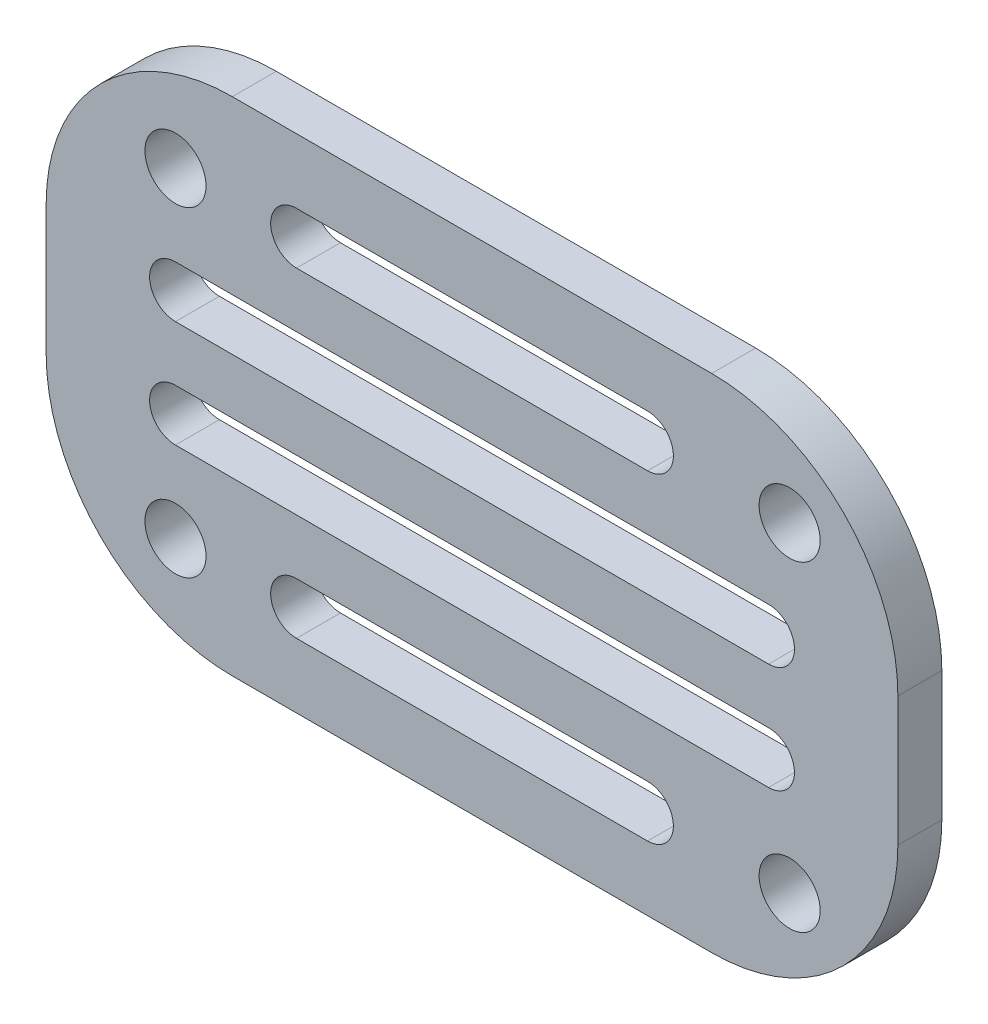
SolidWorks part; units mm, degrees
ref_plane "Front Plane" through (0, 0, 0) normal (0, 0, 1) x (1, 0, 0)
ref_plane "Top Plane" through (0, 0, 0) normal (0, 1, 0) x (1, 0, 0)
ref_plane "Right Plane" through (0, 0, 0) normal (1, 0, 0) x (0, 0, -1)
sketch "Sketch1" plane through (0, 0, 0) normal (0, 0, 1) x (1, 0, 0)
  line L0 (-12.7, -7.874) -> (17.4625, -7.874) construction
  line L5 (20.1005, -9.6408) -> (17.4625, -7.874) construction
  line L6 (-9.906, 12.319) -> (13.6347, 12.319)
  line L7 (17.4625, -7.874) -> (17.4625, 7.874) construction
  line L8 (17.4625, 7.874) -> (-12.7, 7.874) construction
  line L9 (-12.7, 7.874) -> (-12.7, -7.874) construction
  line L10 (-19.05, 3.175) -> (-19.05, -3.175)
  line L11 (-9.906, -12.319) -> (13.6347, -12.319)
  line L12 (22.7787, 3.175) -> (22.7787, -3.175)
  line L15 (6.9386, 0) -> (-6.9386, 0) construction
  circle A0 centre (-12.7, 7.874) radius 1.5
  circle A1 centre (-12.7, -7.874) radius 1.5
  circle A2 centre (17.4625, 7.874) radius 1.5
  circle A3 centre (17.4625, -7.874) radius 1.5
  arc A4 (13.6347, -12.319) -> (22.7787, -3.175) centre (13.6347, -3.175) ccw
  arc A5 (13.6347, 12.319) -> (22.7787, 3.175) centre (13.6347, 3.175) cw
  arc A6 (-9.906, 12.319) -> (-19.05, 3.175) centre (-9.906, 3.175) ccw
  arc A7 (-19.05, -3.175) -> (-9.906, -12.319) centre (-9.906, -3.175) ccw
  point P0 (0, 0)
  point P2 (-12.7, 0)
  point P3 (0, 0)
  dimension "D1" = 3
  dimension "D6" = 6.35
  dimension "D7" = 3.175
  dimension "D2" = 15.748
  dimension "D3" = 17.4625
  dimension "D4" = 4.445
  dimension "D5" = 6.35
  dimension "D9" = 12.7
extrude "Boss-Extrude1" add sketch "Sketch1" along normal blind 2.159
sketch "Sketch4" plane through (0, 0, 2.159) normal (0, 0, 1) x (1, 0, 0)
  line L1 (-6.755, 7.874) -> (10.4837, 7.874) construction
  line L2 (-6.755, 9.144) -> (10.4837, 9.144)
  line L3 (-6.755, 6.604) -> (10.4837, 6.604)
  line L4 (-12.7, 2.6247) -> (16.4287, 2.6247) construction
  line L5 (-12.7, 3.8947) -> (16.4287, 3.8947)
  line L6 (-12.7, 1.3547) -> (16.4287, 1.3547)
  line L7 (-12.7, -2.6247) -> (16.4287, -2.6247) construction
  line L8 (-12.7, -1.3547) -> (16.4287, -1.3547)
  line L9 (-12.7, -3.8947) -> (16.4287, -3.8947)
  line L10 (-6.755, -7.874) -> (10.4837, -7.874) construction
  line L11 (-6.755, -6.604) -> (10.4837, -6.604)
  line L12 (-6.755, -9.144) -> (10.4837, -9.144)
  line L13 (1.8644, 6.604) -> (1.8644, 3.8947) construction
  line L14 (1.8644, 1.3547) -> (1.8644, -1.3547) construction
  line L15 (1.8644, -3.8947) -> (1.8644, -6.604) construction
  line L16 (-9.906, 12.319) -> (13.6347, 12.319) construction
  line L17 (-8.025, 7.874) -> (-11.2, 7.874) construction
  line L18 (22.7787, 3.175) -> (22.7787, -3.175) construction
  line L19 (-12.7, 7.874) -> (-12.7, 2.6247) construction
  arc A3 (-6.755, 9.144) -> (-6.755, 6.604) centre (-6.755, 7.874) ccw
  arc A4 (10.4837, 6.604) -> (10.4837, 9.144) centre (10.4837, 7.874) ccw
  arc A5 (-12.7, 3.8947) -> (-12.7, 1.3547) centre (-12.7, 2.6247) ccw
  arc A6 (16.4287, 1.3547) -> (16.4287, 3.8947) centre (16.4287, 2.6247) ccw
  arc A7 (-12.7, -1.3547) -> (-12.7, -3.8947) centre (-12.7, -2.6247) ccw
  arc A8 (16.4287, -3.8947) -> (16.4287, -1.3547) centre (16.4287, -2.6247) ccw
  arc A9 (-6.755, -6.604) -> (-6.755, -9.144) centre (-6.755, -7.874) ccw
  arc A10 (10.4837, -9.144) -> (10.4837, -6.604) centre (10.4837, -7.874) ccw
  circle A13 centre (-12.7, 7.874) radius 1.5 construction
  point P4 (1.8644, 7.874)
  point P9 (1.8644, 2.6247)
  point P16 (1.8644, -2.6247)
  point P23 (1.8644, -7.874)
  point P32 (9.9103, 7.874)
  point P38 (-11.2, 7.874)
  point P40 (1.8644, 12.319)
  point P45 (-11.2, 7.874)
  point P46 (-7.3577, 7.874)
  point P49 (1.8644, 0)
  point P52 (22.7787, 0)
  dimension "D2" = 1.27
  dimension "D3" = 3.175
  dimension "D1" = 3.175
extrude "Cut-Extrude1" cut sketch "Sketch4" against normal through all
